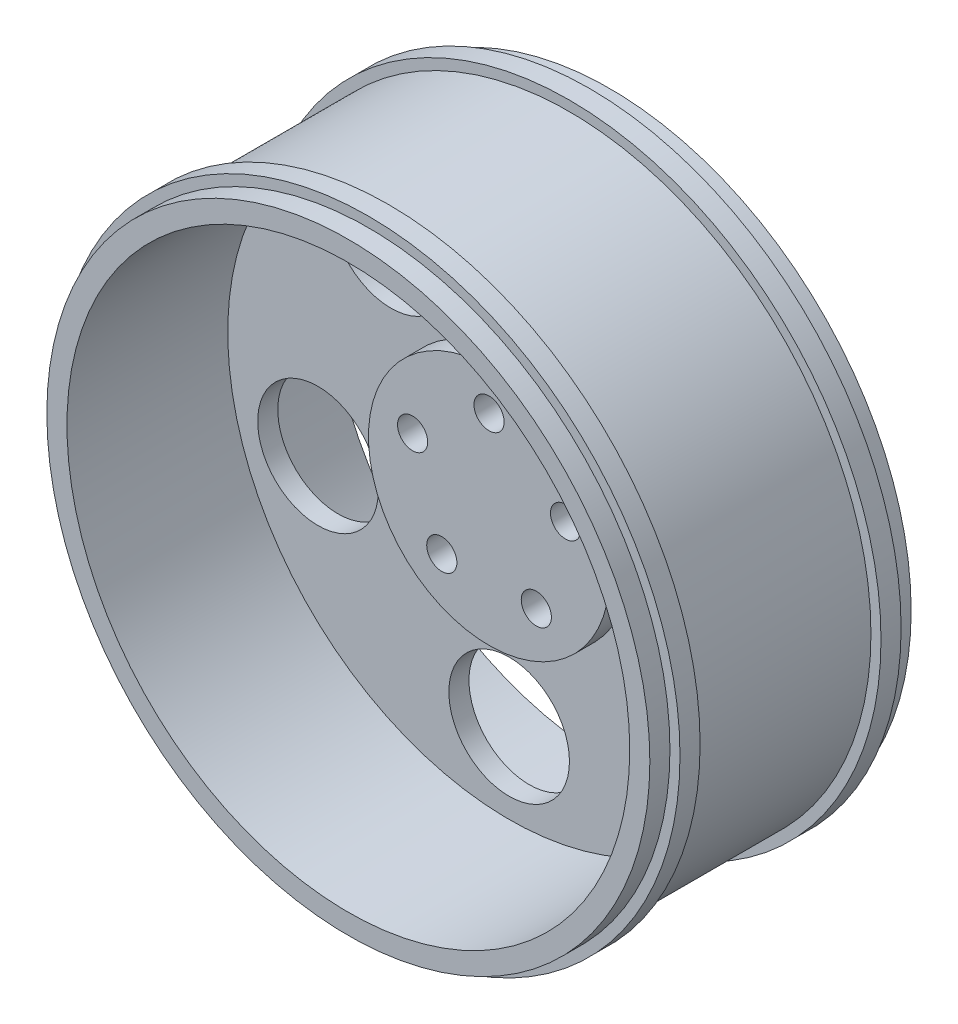
SolidWorks part; units mm, degrees
material "AISI 1020"
ref_plane "Front Plane" through (0, 0, 0) normal (0, 0, 1) x (1, 0, 0)
ref_plane "Top Plane" through (0, 0, 0) normal (0, 1, 0) x (1, 0, 0)
ref_plane "Right Plane" through (0, 0, 0) normal (1, 0, 0) x (0, 0, -1)
sketch "Sketch6" plane through (0, 0, 0) normal (1, 0, 0) x (0, 0, -1)
  line L0 (0, 0) -> (10, 0)
  line L1 (10, 0) -> (10, 140)
  line L2 (10, 140) -> (50, 140)
  line L3 (50, 140) -> (50, 150)
  line L4 (50, 150) -> (40, 150)
  line L5 (40, 150) -> (40, 155)
  line L6 (40, 155) -> (30, 155)
  line L7 (30, 155) -> (30, 150)
  line L8 (30, 150) -> (-60, 150)
  line L9 (-60, 150) -> (-60, 155)
  line L10 (-60, 155) -> (-70, 155)
  line L11 (-70, 155) -> (-70, 150)
  line L12 (-70, 150) -> (-80, 150)
  line L13 (-80, 150) -> (-80, 140)
  line L14 (-80, 140) -> (0, 140)
  line L15 (0, 140) -> (0, 60)
  line L16 (0, 60) -> (-10, 60)
  line L17 (-10, 60) -> (-10, 0)
  line L18 (-10, 0) -> (0, 0)
  dimension "D1" = 150
  dimension "D2" = 10
  dimension "D3" = 10
  dimension "D4" = 60
  dimension "D5" = 10
  dimension "D6" = 10
  dimension "D7" = 10
  dimension "D8" = 5
  dimension "D9" = 10
  dimension "D10" = 10
  dimension "D11" = 5
  dimension "D12" = 130
  dimension "D13" = 40
revolve "Revolve3" add sketch "Sketch6" angle 360 about L18
sketch "Sketch8" plane through (0, 0, 10) normal (0, 0, 1) x (1, 0, 0)
  circle A0 centre (0, 40) radius 7.5
  circle A1 centre (38.0423, 12.3607) radius 7.5
  circle A2 centre (23.5114, -32.3607) radius 7.5
  circle A3 centre (-23.5114, -32.3607) radius 7.5
  circle A4 centre (-38.0423, 12.3607) radius 7.5
  point P14 (0, 0)
  dimension "D1" = 15
  dimension "D2" = 5
  dimension "4" = 40
extrude "Cut-Extrude1" cut sketch "Sketch8" against normal through all both and the other way through all
sketch "Sketch9" plane through (0, 0, 0) normal (0, 0, 1) x (1, 0, 0)
  circle A0 centre (0, -100) radius 30
  circle A1 centre (-95.1057, -30.9017) radius 30
  circle A2 centre (-58.7785, 80.9017) radius 30
  circle A3 centre (58.7785, 80.9017) radius 30
  circle A4 centre (95.1057, -30.9017) radius 30
  point P13 (0, 0)
  dimension "D1" = 60
  dimension "D2" = 100
  dimension "D3" = 5
extrude "Cut-Extrude2" cut sketch "Sketch9" against normal through all both contours A3 | A2 | A1 | A0 | A4
